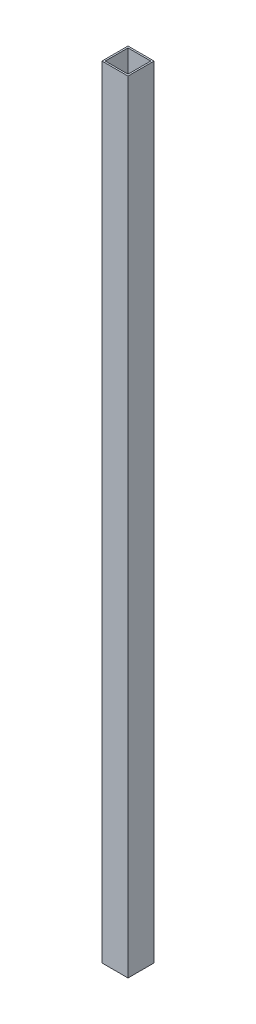
SolidWorks part; units mm, degrees
ref_plane "Front Plane" through (0, 0, 0) normal (0, 0, 1) x (1, 0, 0)
ref_plane "Top Plane" through (0, 0, 0) normal (0, 1, 0) x (1, 0, 0)
ref_plane "Right Plane" through (0, 0, 0) normal (1, 0, 0) x (0, 0, -1)
sketch "Sketch1" plane through (0, 0, 0) normal (0, 1, 0) x (1, 0, 0)
  line L1 (0, 0) -> (25.4, 0)
  line L2 (0, 0) -> (0, 25.4)
  line L3 (0, 25.4) -> (25.4, 25.4)
  line L4 (25.4, 0) -> (25.4, 25.4)
  line L5 (1.6002, 23.7998) -> (23.7998, 23.7998)
  line L6 (1.6002, 23.7998) -> (1.6002, 1.6002)
  line L7 (1.6002, 1.6002) -> (23.7998, 1.6002)
  line L8 (23.7998, 23.7998) -> (23.7998, 1.6002)
  dimension "D1" = 1.6002
  dimension "D2" = 1.6002
  dimension "D3" = 1.6002
  dimension "D4" = 1.6002
  dimension "D5" = 25.4
  dimension "D6" = 25.4
extrude "Boss-Extrude1" add sketch "Sketch1" along normal blind 762
